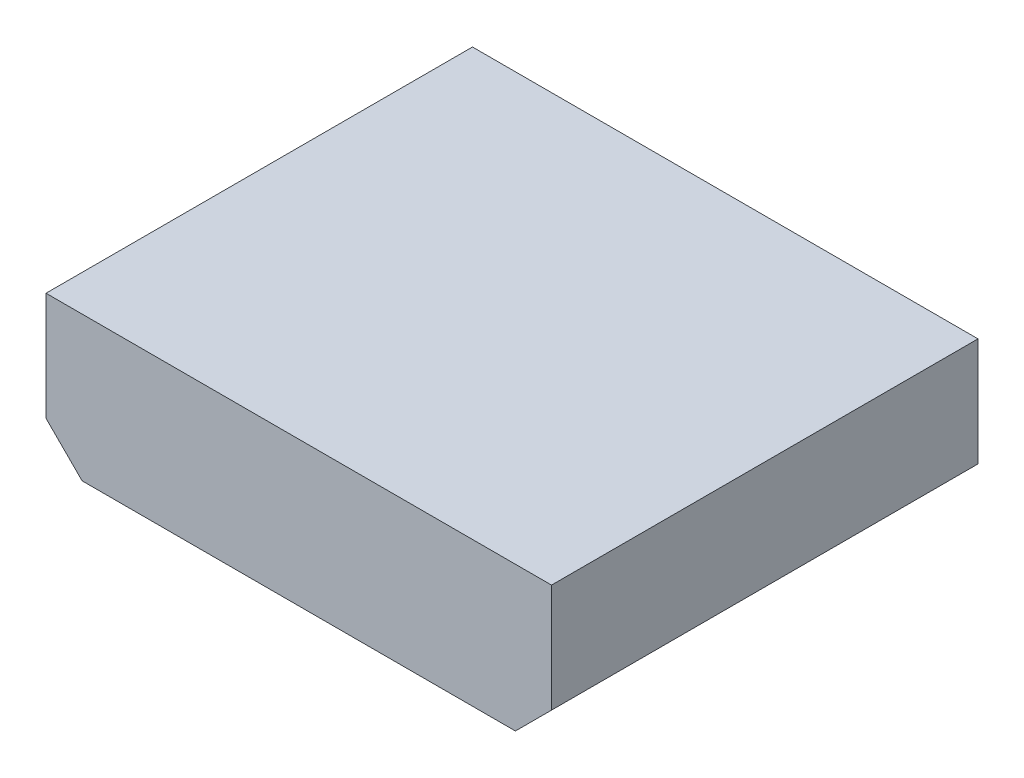
SolidWorks part; units mm, degrees
ref_plane "Front Plane" through (0, 0, 0) normal (0, 0, 1) x (1, 0, 0)
ref_plane "Top Plane" through (0, 0, 0) normal (0, 1, 0) x (1, 0, 0)
ref_plane "Right Plane" through (0, 0, 0) normal (1, 0, 0) x (0, 0, -1)
sketch "Sketch1" plane through (0, 0, 0) normal (0, 0, 1) x (1, 0, 0)
  line L0 (-5.08, 2.54) -> (-5.08, -1.27)
  line L1 (-5.08, -1.27) -> (-3.81, -2.54)
  line L2 (-3.81, -2.54) -> (11.43, -2.54)
  line L3 (11.43, -2.54) -> (12.7, -1.27)
  line L4 (12.7, -1.27) -> (12.7, 2.54)
  line L5 (12.7, 2.54) -> (-5.08, 2.54)
extrude "Component_Outline" add sketch "Sketch1" along normal blind 15 separate body
sketch "Sketch2" plane through (0, 0, 0) normal (0, 0, 1) x (1, 0, 0)
  circle A0 centre (0, 0) radius 0.25
extrude "1" add sketch "Sketch2" against normal blind 2 separate body
sketch "Sketch3" plane through (0, 0, 0) normal (0, 0, 1) x (1, 0, 0)
  circle A0 centre (2.54, 0) radius 0.25
extrude "2" add sketch "Sketch3" against normal blind 2 separate body
sketch "Sketch4" plane through (0, 0, 0) normal (0, 0, 1) x (1, 0, 0)
  circle A0 centre (5.08, 0) radius 0.25
extrude "3" add sketch "Sketch4" against normal blind 2 separate body
sketch "Sketch5" plane through (0, 0, 0) normal (0, 0, 1) x (1, 0, 0)
  circle A0 centre (7.62, 0) radius 0.25
extrude "4" add sketch "Sketch5" against normal blind 2 separate body
sketch3d "3DSketch1"
  line L0 (0, 0, 0) -> (1, 0, 0)
  line L1 (0, 0, 0) -> (0, 1, 0)
  line L2 (0, 0, 0) -> (0, 0, 1)
  point P0 (0, 0, 0)
